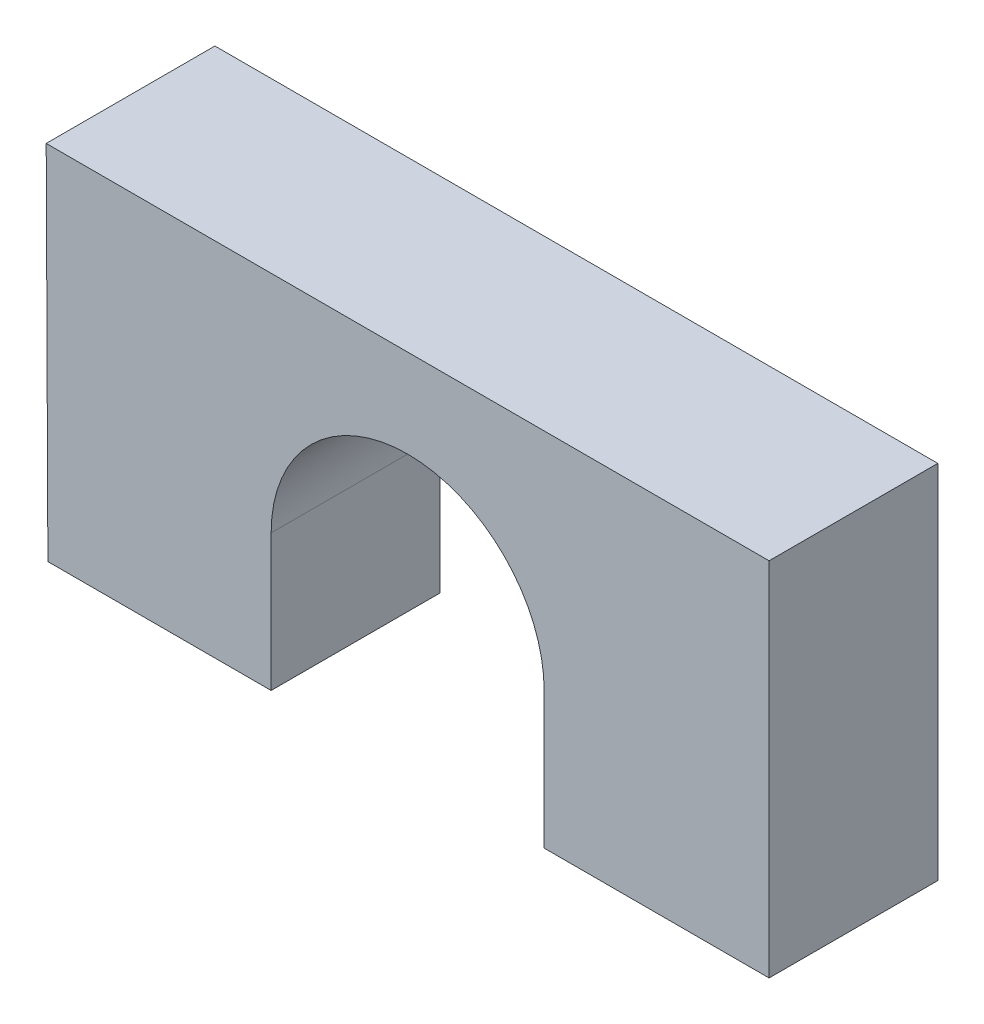
SolidWorks part; units mm, degrees
ref_plane "Front Plane" through (0, 0, 0) normal (0, 0, 1) x (1, 0, 0)
ref_plane "Top Plane" through (0, 0, 0) normal (0, 1, 0) x (1, 0, 0)
ref_plane "Right Plane" through (0, 0, 0) normal (1, 0, 0) x (0, 0, -1)
sketch "Sketch1" plane through (0, 0, 0) normal (0, 0, 1) x (1, 0, 0)
  line L0 (4.855, 0) -> (-22.7506, 0) construction
  line L1 (-4.855, -4.855) -> (-20.7346, -4.855) construction
  line L2 (-12.855, 7.9958) -> (-12.7948, -4.855)
  line L3 (12.855, 7.9958) -> (12.855, -4.855)
  line L4 (-12.855, 7.9958) -> (12.855, 7.9958)
  line L5 (-4.855, 0) -> (-4.855, -4.855)
  line L6 (-4.855, -4.855) -> (-12.7948, -4.855)
  line L7 (4.855, 0) -> (4.855, -4.855)
  line L8 (4.855, -4.855) -> (12.855, -4.855)
  arc A0 (4.855, 0) -> (-4.855, 0) centre (0, 0) ccw
  dimension "D1" = 9.71
  dimension "D2" = 25.71
  dimension "D3" = 12.8508
  dimension "D4" = 7.9398
  dimension "D5" = 7.9625
extrude "Boss-Extrude2" add sketch "Sketch1" along normal blind 6
